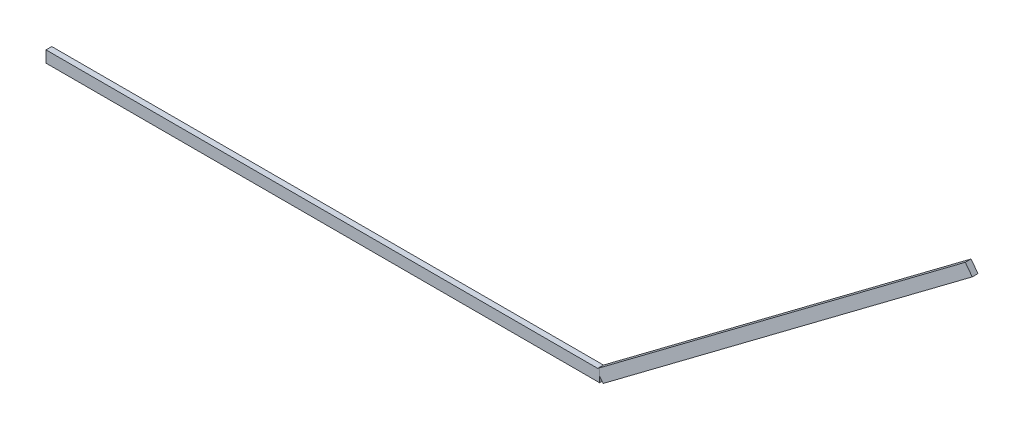
SolidWorks part; units mm, degrees
material "6061-T6 (SS)"
ref_plane "Front" through (0, 0, 0) normal (0, 0, 1) x (1, 0, 0)
ref_plane "Top" through (0, 0, 0) normal (0, 1, 0) x (1, 0, 0)
ref_plane "Right" through (0, 0, 0) normal (1, 0, 0) x (0, 0, -1)
sketch "Sketch2" plane through (0, 0, 0) normal (0, 0, 1) x (1, 0, 0)
  line L0 (0, 0) -> (1828.8, 0)
  line L1 (1828.8, 0) -> (3048, 914.4)
  point P3 (914.4, 0)
  dimension "D1" = 1828.8
  dimension "D2" = 1219.2
  dimension "D3" = 914.4
  dimension "D4" = 914.4
ref_plane "Plane1" through (0, 0, 0) normal (1, 0, 0) x (0, 1, 0)
ref_plane "Plane2" through (1828.8, 0, 0) normal (0.8, 0.6, 0) x (-0.6, 0.8, 0)
ref_plane "Plane3" through (0, 0, 0) normal (1, 0, 0) x (0, 1, 0)
other " C:\\PROGRAM FILES\\SOLIDWORKS CORP\\SOLIDWORKS\\LANG\\ENGLISH\\WELDMENT PROFILES\\CUSTOM\\ENGLISH\\1.5 BY .75 IN REC 2 - IS MISSING(1)"
ref_plane "Plane4" through (0, 0, 0) normal (1, 0, 0) x (0, 0, 1)
sketch "Sketch1" plane through (0, 0, 0) normal (1, 0, 0) x (0, 0, 1)
  line L1 (-9.525, -19.05) -> (9.525, -19.05)
  line L2 (-9.525, -19.05) -> (-9.525, 19.05)
  line L3 (-9.525, 19.05) -> (9.525, 19.05)
  line L4 (9.525, -19.05) -> (9.525, 19.05)
  line L5 (-9.525, -19.05) -> (9.525, 19.05) construction
  line L6 (-9.525, 19.05) -> (9.525, -19.05) construction
  point P0 (0, 0)
  point P6 (0, 0)
  dimension "D1" = 38.1
  dimension "D2" = 19.05
ref_point "Point1"
